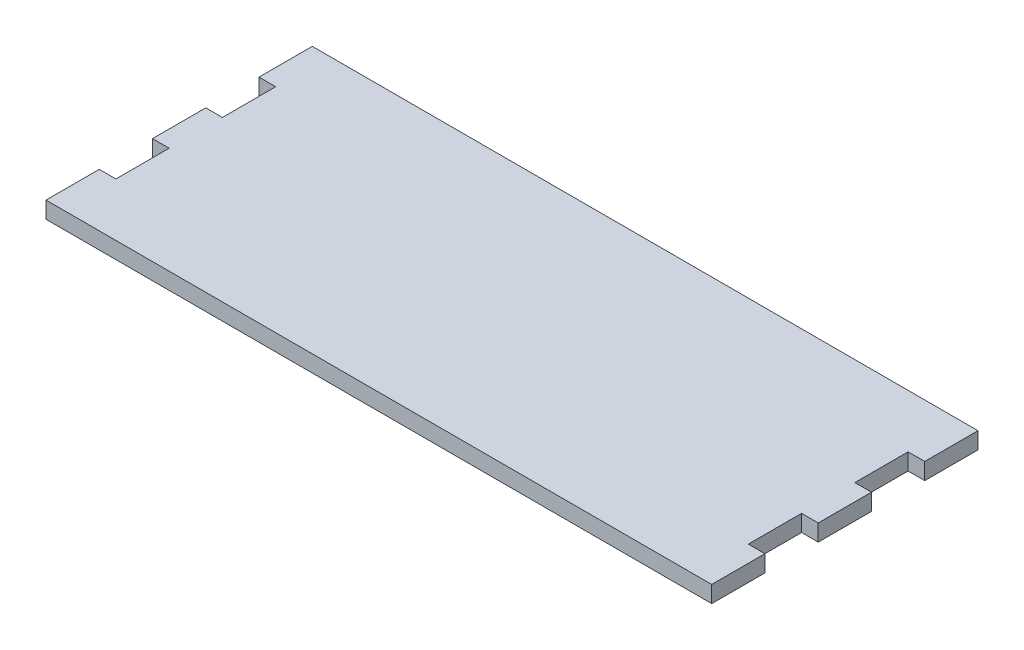
SolidWorks part; units mm, degrees
ref_plane "Front Plane" through (0, 0, 0) normal (0, 0, 1) x (1, 0, 0)
ref_plane "Top Plane" through (0, 0, 0) normal (0, 1, 0) x (1, 0, 0)
ref_plane "Right Plane" through (0, 0, 0) normal (1, 0, 0) x (0, 0, -1)
sketch "Sketch1" plane through (0, 0, 0) normal (0, 1, 0) x (1, 0, 0)
  line L0 (-95, 24) -> (-95, 8)
  line L1 (-100, 40) -> (100, 40)
  line L2 (-100, 40) -> (-100, 24)
  line L3 (-100, -40) -> (100, -40)
  line L4 (100, 40) -> (100, 24)
  line L5 (-100, 40) -> (100, -40) construction
  line L6 (-100, -40) -> (100, 40) construction
  line L7 (100, 8) -> (100, -8)
  line L9 (-100, 8) -> (-100, -8)
  line L11 (-100, -24) -> (-100, -40)
  line L12 (95, 24) -> (95, 8)
  line L13 (100, -24) -> (100, -40)
  line L15 (95, -8) -> (95, -24)
  line L17 (-100, 24) -> (-95, 24)
  line L18 (-100, 8) -> (-95, 8)
  line L19 (-100, -8) -> (-95, -8)
  line L20 (-100, -24) -> (-95, -24)
  line L21 (95, 24) -> (100, 24)
  line L22 (95, 8) -> (100, 8)
  line L23 (95, -8) -> (100, -8)
  line L24 (95, -24) -> (100, -24)
  line L26 (-95, -8) -> (-95, -24)
  point P0 (0, 0)
  dimension "D1" = 200
  dimension "D2" = 80
  dimension "D3" = 5
  dimension "D4" = 5
  dimension "D5" = 5
  dimension "D6" = 5
extrude "Boss-Extrude1" add sketch "Sketch1" along normal blind 5
